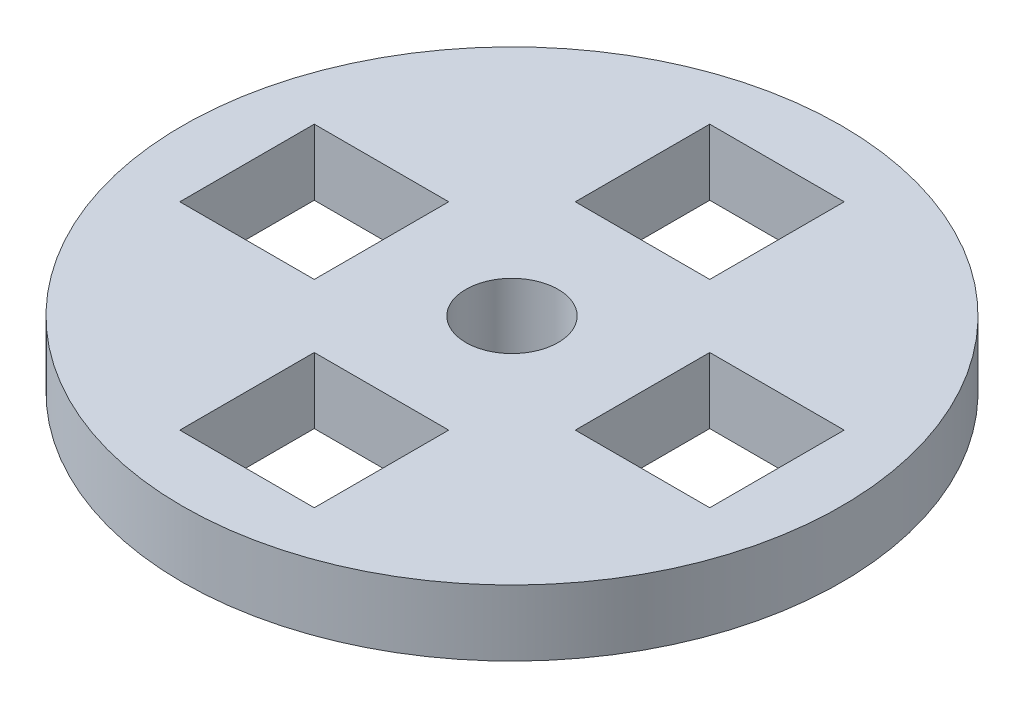
SolidWorks part; units mm, degrees
ref_plane "Alzado" through (0, 0, 0) normal (0, 0, 1) x (1, 0, 0)
ref_plane "Planta" through (0, 0, 0) normal (0, 1, 0) x (1, 0, 0)
ref_plane "Vista lateral" through (0, 0, 0) normal (1, 0, 0) x (0, 0, -1)
sketch "Croquis1" plane through (0, 0, 0) normal (0, 1, 0) x (1, 0, 0)
  line L0 (-15, 0) -> (15, 0) construction
  line L2 (-20.1, 5.1) -> (-9.9, 5.1)
  line L3 (-20.1, 5.1) -> (-20.1, -5.1)
  line L4 (-20.1, -5.1) -> (-9.9, -5.1)
  line L5 (-9.9, 5.1) -> (-9.9, -5.1)
  line L6 (-20.1, 5.1) -> (-9.9, -5.1) construction
  line L7 (-20.1, -5.1) -> (-9.9, 5.1) construction
  line L8 (20.1, 5.1) -> (9.9, 5.1)
  line L9 (20.1, 5.1) -> (20.1, -5.1)
  line L10 (20.1, -5.1) -> (9.9, -5.1)
  line L11 (9.9, 5.1) -> (9.9, -5.1)
  line L12 (20.1, 5.1) -> (9.9, -5.1) construction
  line L13 (20.1, -5.1) -> (9.9, 5.1) construction
  line L15 (0, -15) -> (0, 15) construction
  line L17 (-5.1, 20.1) -> (5.1, 20.1)
  line L18 (-5.1, 20.1) -> (-5.1, 9.9)
  line L19 (-5.1, 9.9) -> (5.1, 9.9)
  line L20 (5.1, 20.1) -> (5.1, 9.9)
  line L21 (-5.1, 20.1) -> (5.1, 9.9) construction
  line L22 (-5.1, 9.9) -> (5.1, 20.1) construction
  line L23 (-5.1, -9.9) -> (5.1, -9.9)
  line L24 (-5.1, -9.9) -> (-5.1, -20.1)
  line L25 (-5.1, -20.1) -> (5.1, -20.1)
  line L26 (5.1, -9.9) -> (5.1, -20.1)
  line L27 (-5.1, -9.9) -> (5.1, -20.1) construction
  line L28 (-5.1, -20.1) -> (5.1, -9.9) construction
  circle A0 centre (0, 0) radius 25
  point P6 (0, 0)
  point P18 (0, 0)
  dimension "D1" = 50
  dimension "D2" = 30
  dimension "D3" = 10.2
  dimension "D4" = 10.2
  dimension "D5" = 10.2
  dimension "D7" = 30
  dimension "D8" = 10.2
  dimension "D9" = 10.2
  dimension "D10" = 10.2
  dimension "D11" = 10.2
  dimension "D12" = 10.2
extrude "Saliente-Extruir1" add sketch "Croquis1" along normal blind 5
sketch "Croquis2" plane through (0, 5, 0) normal (0, 1, 0) x (1, 0, 0)
  circle A0 centre (0, 0) radius 3.5
  dimension "D1" = 7
extrude "Cortar-Extruir1" cut sketch "Croquis2" against normal blind 47
